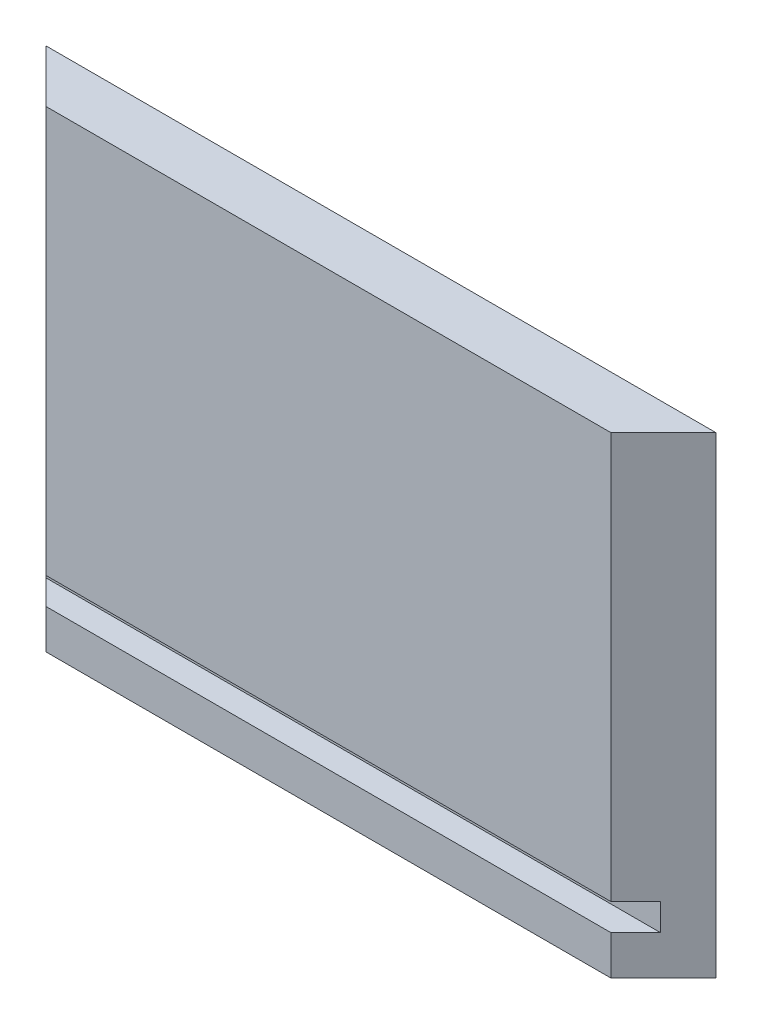
SolidWorks part; units mm, degrees
ref_plane "Front Plane" through (0, 0, 0) normal (0, 0, 1) x (1, 0, 0)
ref_plane "Top Plane" through (0, 0, 0) normal (0, 1, 0) x (1, 0, 0)
ref_plane "Right Plane" through (0, 0, 0) normal (1, 0, 0) x (0, 0, -1)
other "Configuration Table"
sketch "Sketch1" plane through (0, 0, 0) normal (0, 1, 0) x (1, 0, 0)
  line L0 (0, 0) -> (81.0006, 0)
  line L1 (81.0006, 0) -> (74.6506, -6.35)
  line L2 (74.6506, -6.35) -> (6.35, -6.35)
  line L3 (6.35, -6.35) -> (0, 0)
  dimension "D1" = 45
  dimension "D2" = 81.0006
  dimension "D3" = 45
  dimension "D4" = 6.35
extrude "Boss-Extrude1" add sketch "Sketch1" along normal blind 57.15
sketch "Sketch2" plane through (0, 0, 0) normal (1, 0, 0) x (0, 0, -1)
  line L0 (-6.35, 4.7625) -> (-3.3528, 4.7625)
  line L1 (-6.35, 57.15) -> (-6.35, 0) construction
  line L2 (-3.3528, 4.7625) -> (-3.3528, 8.0137)
  line L3 (-3.3528, 8.0137) -> (-6.35, 8.0137)
  line L4 (-6.35, 8.0137) -> (-6.35, 4.7625)
  line L5 (-6.35, 0) -> (0, 0) construction
  dimension "D1" = 4.7625
  dimension "D2" = 3.2512
  dimension "D3" = 2.9972
extrude "Cut-Extrude1" cut sketch "Sketch2" against normal through all and the other way through all
